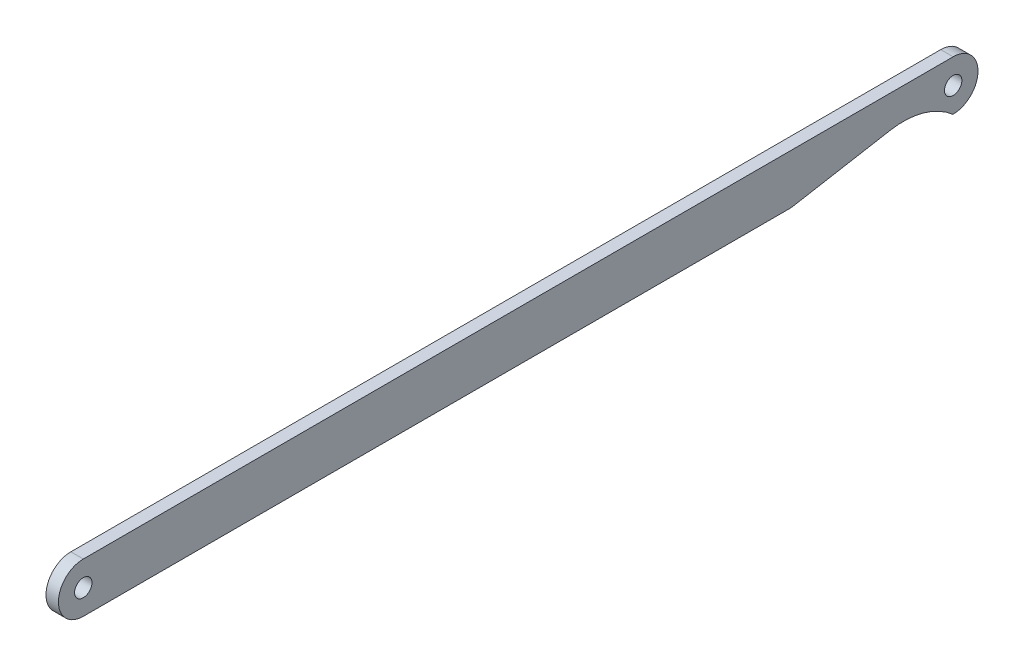
SolidWorks part; units mm, degrees
material "2024-T4"
ref_plane "Front" through (0, 0, 0) normal (0, 0, 1) x (1, 0, 0)
ref_plane "Top" through (0, 0, 0) normal (0, 1, 0) x (1, 0, 0)
ref_plane "Right" through (0, 0, 0) normal (1, 0, 0) x (0, 0, -1)
sketch "Эскиз1" plane through (0, 0, 0) normal (1, 0, 0) x (0, 0, -1)
  line L0 (0, 0) -> (70, 0)
  line L2 (-2, -2) -> (-2, 11.811) construction
  line L4 (70, -4) -> (0, -4)
  circle A0 centre (0, -2) radius 0.7
  circle A1 centre (70, -2) radius 0.7
  arc A2 (0, 0) -> (0, -4) centre (0, -2) ccw
  arc A3 (70, 0) -> (70, -4) centre (70, -2) cw
  dimension "D1" = 70
  dimension "D9" = 1.4
  dimension "D8" = 4
extrude "Вытянуть1" add sketch "Эскиз1" along normal blind 1
sketch "Эскиз2" plane through (1, 0, 0) normal (1, 0, 0) x (0, 0, -1)
  line L0 (64.9581, -2.5912) -> (56.9681, -4)
  line L1 (0, -4) -> (70, -4) construction
  line L2 (70, 0) -> (0, 0) construction
  line L3 (66, -2.5) -> (55.1017, -2.5) construction
  arc A0 (64.9581, -2.5912) -> (69.9686, -4) centre (66, -8.5) cw
  circle A2 centre (70, -2) radius 0.7 construction
  point P0 (70, -2)
  dimension "D1" = 10
  dimension "D2" = 6
  dimension "D3" = 1.5
  dimension "D4" = 4
extrude "Вырез-Вытянуть1" cut sketch "Эскиз2" against normal through all
